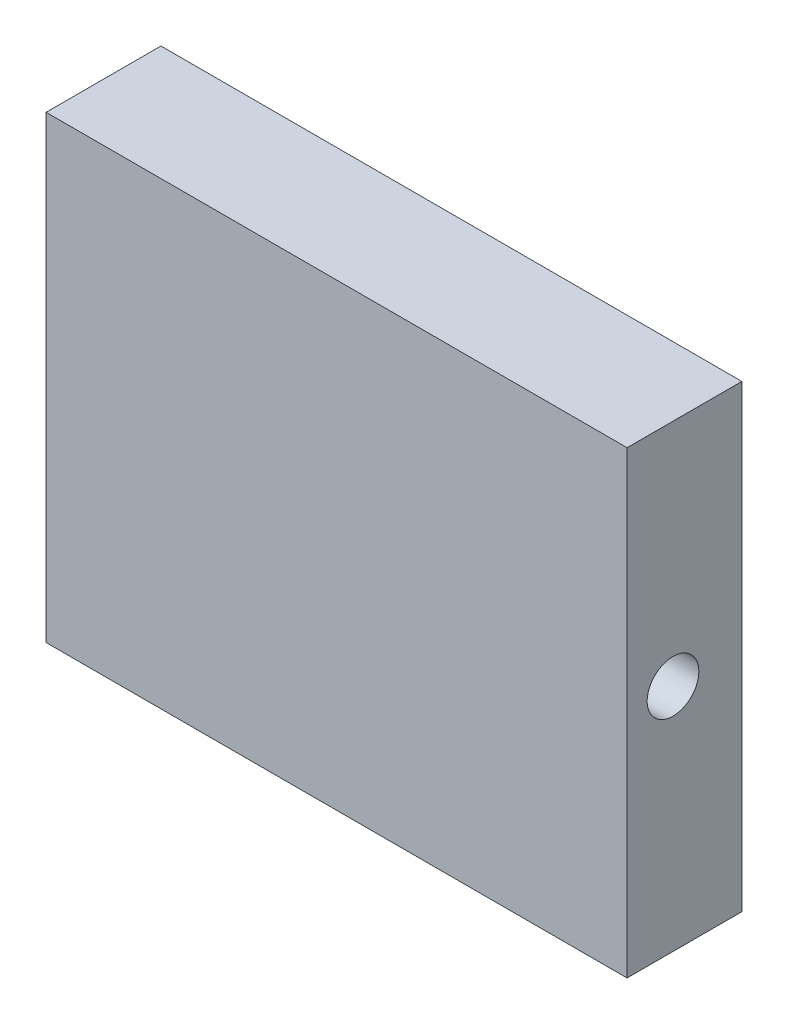
SolidWorks part; units mm, degrees
ref_plane "Front" through (0, 0, 0) normal (0, 0, 1) x (1, 0, 0)
ref_plane "Top" through (0, 0, 0) normal (0, 1, 0) x (1, 0, 0)
ref_plane "Right" through (0, 0, 0) normal (1, 0, 0) x (0, 0, -1)
sketch "Sketch1" plane through (0, 0, 0) normal (0, 0, 1) x (1, 0, 0)
  line L0 (50.6, 22.5) -> (50.6, 17.5) construction
  line L1 (0, 0) -> (50.6, 0)
  line L2 (0, 0) -> (0, 40)
  line L3 (0, 40) -> (50.6, 40)
  line L4 (50.6, 0) -> (50.6, 40)
  line L5 (1000.6, 17.5) -> (1000.6, 22.5) construction
  dimension "D1" = 50.6
  dimension "D2" = 40
extrude "Extrude1" add sketch "Sketch1" along normal blind 10
sketch "Sketch2" plane through (50.6, 0, 0) normal (1, 0, 0) x (0, 0, -1)
  circle A0 centre (-6, 20) radius 2.25
extrude "Cut-Extrude1" cut sketch "Sketch2" against normal blind 10
